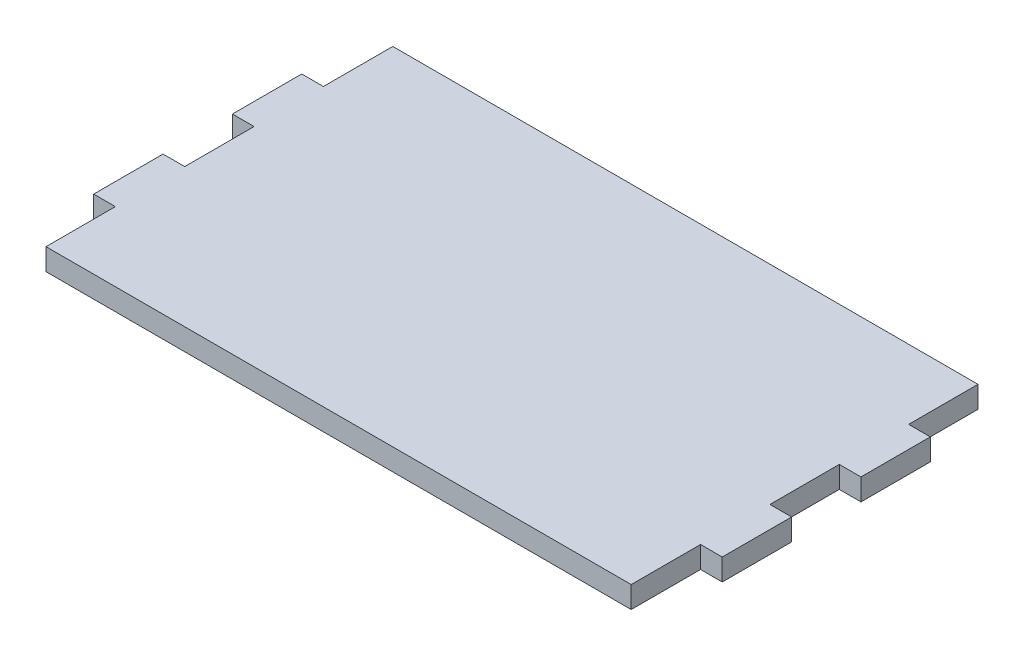
SolidWorks part; units mm, degrees
ref_plane "Front Plane" through (0, 0, 0) normal (0, 0, 1) x (1, 0, 0)
ref_plane "Top Plane" through (0, 0, 0) normal (0, 1, 0) x (1, 0, 0)
ref_plane "Right Plane" through (0, 0, 0) normal (1, 0, 0) x (0, 0, -1)
sketch "Sketch1" plane through (0, 0, 0) normal (0, 1, 0) x (1, 0, 0)
  line L0 (-67.5, 40) -> (-67.5, 24)
  line L1 (-67.5, 40) -> (67.5, 40)
  line L3 (-67.5, -40) -> (67.5, -40)
  line L4 (72.5, 24) -> (72.5, 8)
  line L5 (-72.5, 40) -> (67.5, -37.2414) construction
  line L6 (-72.5, -40) -> (72.5, 40) construction
  line L7 (67.5, 40) -> (67.5, 24)
  line L8 (-72.5, 24) -> (-72.5, 8)
  line L10 (-72.5, -8) -> (-72.5, -24)
  line L13 (67.5, 40) -> (67.5, -40) construction
  line L14 (67.5, 8) -> (67.5, -8)
  line L15 (72.5, -8) -> (72.5, -24)
  line L16 (67.5, -24) -> (67.5, -40)
  line L17 (-72.5, 24) -> (-67.5, 24)
  line L18 (-72.5, 8) -> (-67.5, 8)
  line L19 (-72.5, -8) -> (-67.5, -8)
  line L20 (-72.5, -24) -> (-67.5, -24)
  line L21 (67.5, 24) -> (72.5, 24)
  line L22 (67.5, 8) -> (72.5, 8)
  line L23 (67.5, -8) -> (72.5, -8)
  line L24 (67.5, -24) -> (72.5, -24)
  line L25 (-67.5, 8) -> (-67.5, -8)
  line L26 (-67.5, 40) -> (-67.5, -40) construction
  line L27 (-67.5, -24) -> (-67.5, -40)
  point P0 (0, 0)
  dimension "D1" = 145
  dimension "D2" = 80
extrude "Boss-Extrude1" add sketch "Sketch1" along normal blind 5
